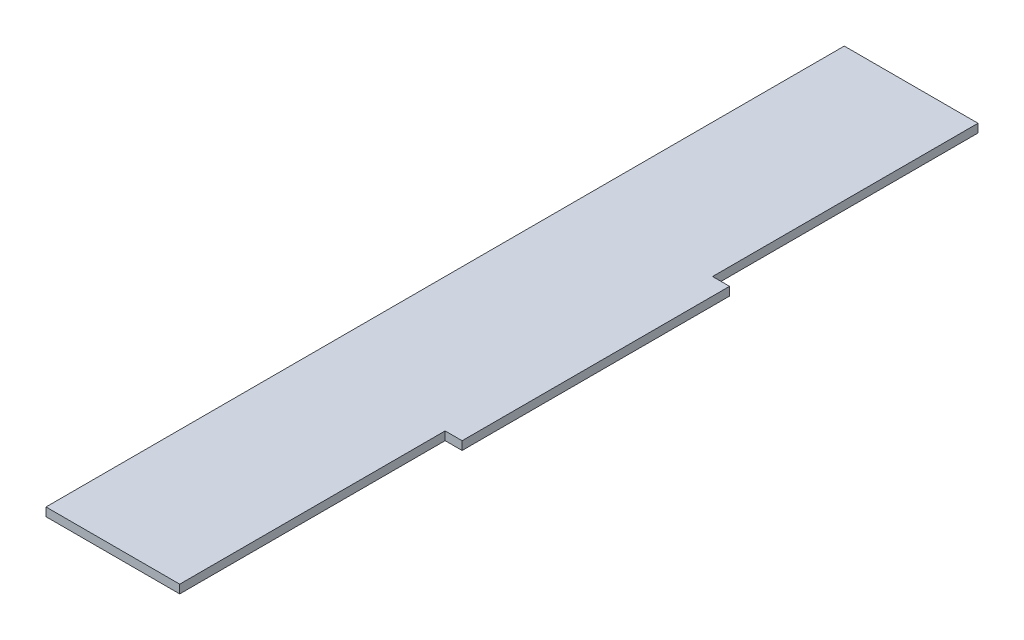
SolidWorks part; units mm, degrees
ref_plane "Front Plane" through (0, 0, 0) normal (0, 0, 1) x (1, 0, 0)
ref_plane "Top Plane" through (0, 0, 0) normal (0, 1, 0) x (1, 0, 0)
ref_plane "Right Plane" through (0, 0, 0) normal (1, 0, 0) x (0, 0, -1)
sketch "Sketch1" plane through (0, 0, 0) normal (0, 1, 0) x (1, 0, 0)
  line L0 (-25, 99.25) -> (25, 99.25)
  line L1 (25, 99.25) -> (25, 0)
  line L2 (25, 0) -> (31.35, 0)
  line L3 (31.35, 0) -> (31.35, -100)
  line L4 (31.35, -100) -> (25, -100)
  line L5 (25, -100) -> (25, -199.25)
  line L6 (25, -199.25) -> (-25, -199.25)
  line L7 (-25, -199.25) -> (-25, -100)
  line L8 (-25, -100) -> (-31.35, -100)
  line L9 (-31.35, -100) -> (-31.35, 0)
  line L10 (-31.35, 0) -> (-25, 0)
  line L11 (-25, 0) -> (-25, 99.25)
  line L12 (-25, 0) -> (-25, -100) construction
  point P11 (0, 99.25)
  point P14 (-31.35, -50)
  dimension "D1" = 6.35
  dimension "D2" = 100
  dimension "D3" = 50
  dimension "D4" = 298.5
extrude "Boss-Extrude1" add sketch "Sketch1" along normal blind 3.175 contours L11 L12 L7 L6 L5 L4 L3 L2 L1 L0
equation "\"length\"= 298.5mm"
equation "\"w_mach\"= 50mm"
equation "\"w_tab\"= 100mm"
equation "\"t_wood\"= 0.125in"
equation "\"t_side\"= 0.25in"
equation "\"D1@Sketch1\"=\"t_side\""
equation "\"D2@Sketch1\"=\"w_tab\""
equation "\"D3@Sketch1\"=\"w_mach\""
equation "\"D4@Sketch1\"=\"length\""
equation "\"D1@Boss-Extrude1\"=\"t_wood\""
